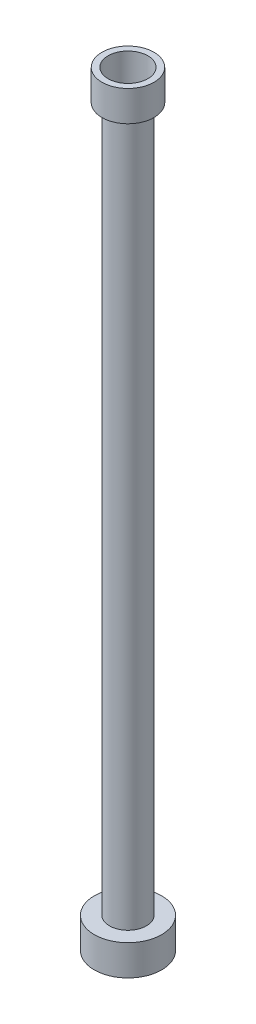
SolidWorks part; units mm, degrees
ref_plane "前视基准面" through (0, 0, 0) normal (0, 0, 1) x (1, 0, 0)
ref_plane "上视基准面" through (0, 0, 0) normal (0, 1, 0) x (1, 0, 0)
ref_plane "右视基准面" through (0, 0, 0) normal (1, 0, 0) x (0, 0, -1)
sketch "草图1" plane through (0, 0, 0) normal (0, 1, 0) x (1, 0, 0)
  circle A0 centre (0, 0) radius 22
  dimension "D1" = 44
extrude "凸台-拉伸1" add sketch "草图1" along normal blind 20
sketch "草图2" plane through (0, 20, 0) normal (0, 1, 0) x (1, 0, 0)
  circle A0 centre (0, 0) radius 12.0798
extrude "凸台-拉伸2" add sketch "草图2" along normal blind 460
sketch "草图3" plane through (0, 480, 0) normal (0, 1, 0) x (1, 0, 0)
  circle A0 centre (0, 0) radius 17
  dimension "D1" = 34
extrude "凸台-拉伸3" add sketch "草图3" along normal blind 20
sketch "草图4" plane through (0, 0, 0) normal (0, -1, 0) x (1, 0, 0)
  circle A0 centre (0, 0) radius 8
  dimension "D1" = 16
extrude "切除-拉伸1" cut sketch "草图4" against normal through all
sketch "草图5" plane through (0, 500, 0) normal (0, 1, 0) x (1, 0, 0)
  circle A0 centre (0, 0) radius 13
  dimension "D1" = 26
extrude "切除-拉伸2" cut sketch "草图5" against normal blind 19
